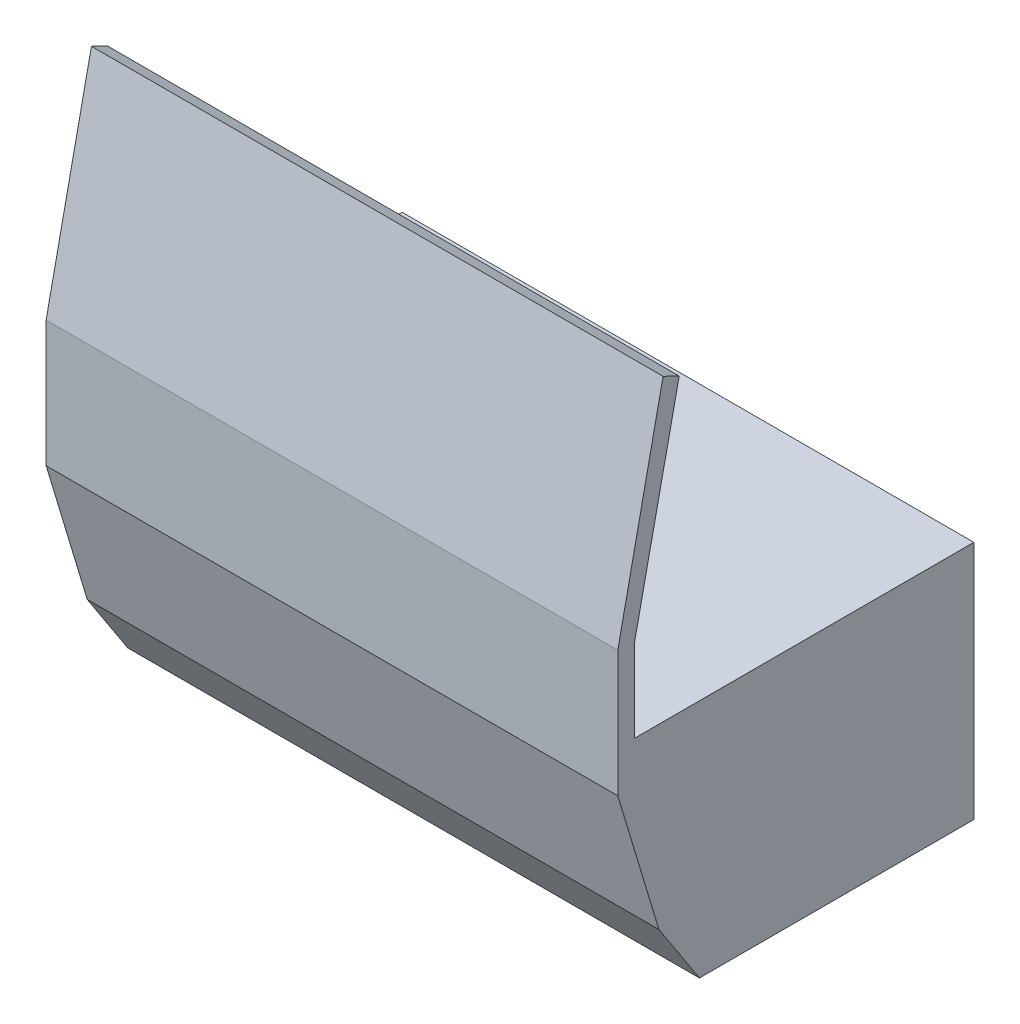
SolidWorks part; units mm, degrees
ref_plane "Front Plane" through (0, 0, 0) normal (0, 0, 1) x (1, 0, 0)
ref_plane "Top Plane" through (0, 0, 0) normal (0, 1, 0) x (1, 0, 0)
ref_plane "Right Plane" through (0, 0, 0) normal (1, 0, 0) x (0, 0, -1)
sketch "Sketch1" plane through (0, 0, 0) normal (0, 0, 1) x (1, 0, 0)
  line L0 (0, 0) -> (-2500, 0)
  line L1 (-2500, 0) -> (-2500, 1050)
  line L2 (-2500, 1050) -> (0, 1050)
  line L3 (0, 1050) -> (0, 0)
  dimension "D1" = 1050
  dimension "D2" = 2500
extrude "Boss-Extrude1" add sketch "Sketch1" along normal blind 1200
shell "Shell2" thickness 20
sketch "Sketch2" plane through (0, 0, 0) normal (1, 0, 0) x (0, 0, -1)
  line L1 (-1200, 0) -> (-1200, 1050) construction
  line L5 (-1200, 1050) -> (-1483.9737, 1050)
  line L9 (-1377.2463, 272.1412) -> (-1200, 0)
  line L11 (-1200, 0) -> (-1200, 1050)
  line L13 (-1483.9737, 1050) -> (-1483.9737, 1412.8818)
  line L15 (-1483.9737, 1412.8818) -> (-1288.6232, 2324.1131)
  line L17 (-1288.6232, 2324.1131) -> (-1359.1455, 2358.3938)
  line L18 (-1359.1455, 2358.3938) -> (-1557.19, 1420.5278)
  line L19 (-1557.19, 1420.5278) -> (-1557.19, 1050)
  line L20 (-1557.19, 868.7102) -> (-1557.19, 1050)
  line L21 (-1377.2463, 272.1412) -> (-1557.19, 868.7102)
extrude "Boss-Extrude2" add sketch "Sketch2" against normal blind 2500
ref_plane "Plane1" through (0, 0, 500) normal (0, 0, 1) x (1, 0, 0)
